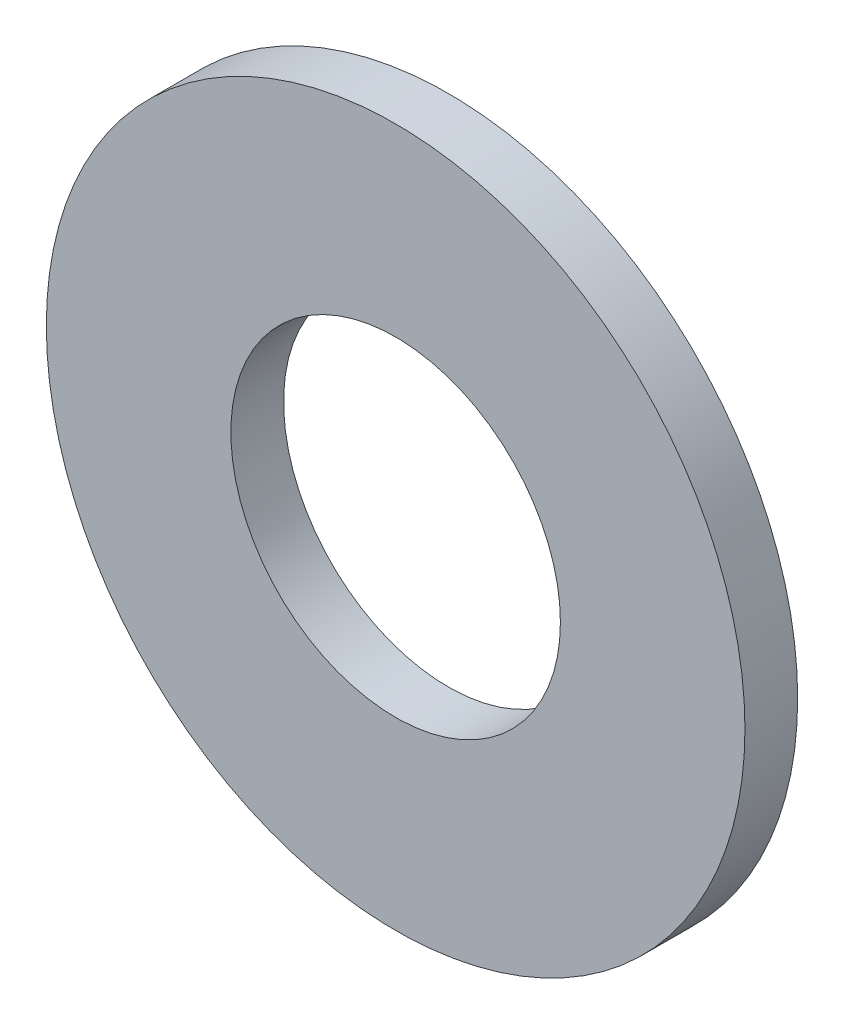
SolidWorks part; units mm, degrees
ref_plane "Front Plane" through (0, 0, 0) normal (0, 0, 1) x (1, 0, 0)
ref_plane "Top Plane" through (0, 0, 0) normal (0, 1, 0) x (1, 0, 0)
ref_plane "Right Plane" through (0, 0, 0) normal (1, 0, 0) x (0, 0, -1)
sketch "Sketch1" plane through (0, 0, 0) normal (0, 0, 1) x (1, 0, 0)
  circle A0 centre (0, 0) radius 6.25
  circle A1 centre (0, 0) radius 13.25
  dimension "D1" = 12.5
  dimension "D2" = 7
extrude "Boss-Extrude1" add sketch "Sketch1" along normal mid plane 2
